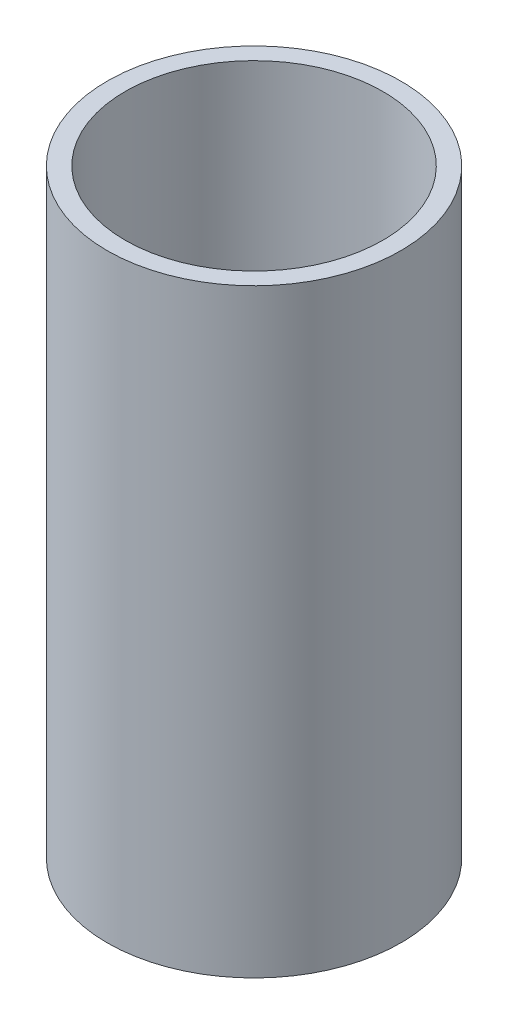
SolidWorks part; units mm, degrees
ref_plane "Front Plane" through (0, 0, 0) normal (0, 0, 1) x (1, 0, 0)
ref_plane "Top Plane" through (0, 0, 0) normal (0, 1, 0) x (1, 0, 0)
ref_plane "Right Plane" through (0, 0, 0) normal (1, 0, 0) x (0, 0, -1)
sketch "Sketch1" plane through (0, 0, 0) normal (0, 1, 0) x (1, 0, 0)
  circle A0 centre (0, 0) radius 4.9
extrude "Boss-Extrude1" add sketch "Sketch1" against normal blind 20
sketch "Sketch2" plane through (0, 0, 0) normal (0, 1, 0) x (1, 0, 0)
  circle A0 centre (0, 0) radius 4.3
extrude "Cut-Extrude1" cut sketch "Sketch2" against normal blind 19.5
